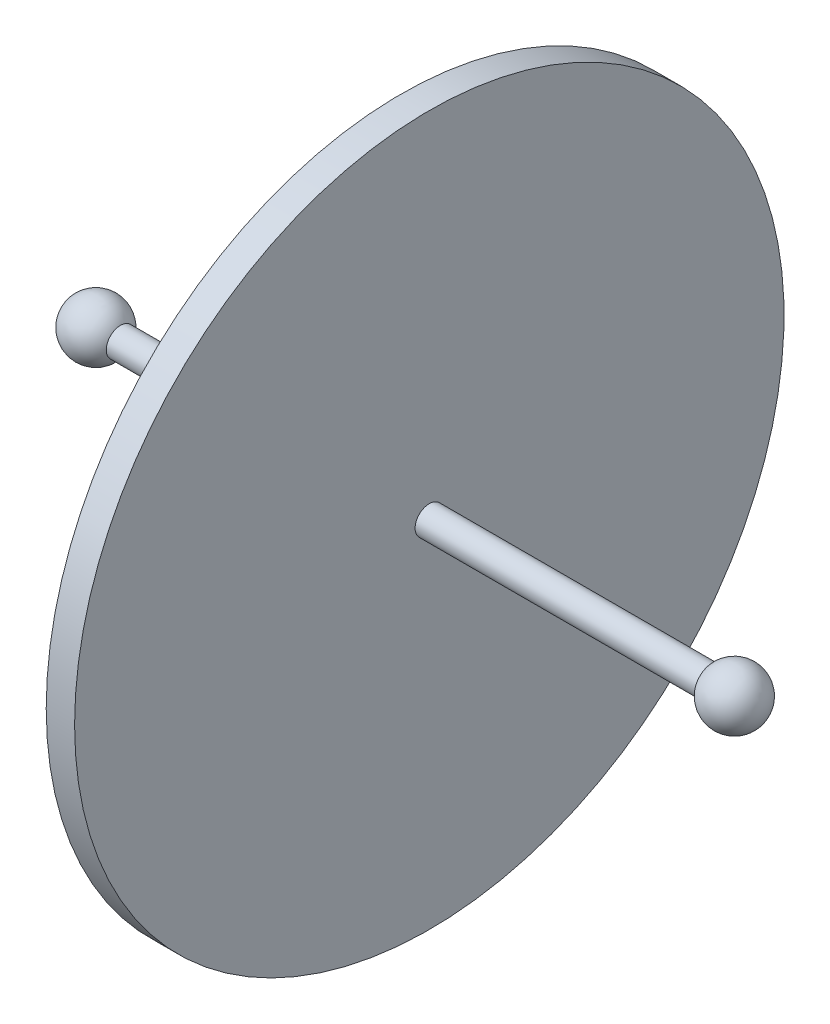
SolidWorks part; units mm, degrees
ref_plane "Plan de face" through (0, 0, 0) normal (0, 0, 1) x (1, 0, 0)
ref_plane "Plan de dessus" through (0, 0, 0) normal (0, 1, 0) x (1, 0, 0)
ref_plane "Plan de droite" through (0, 0, 0) normal (1, 0, 0) x (0, 0, -1)
sketch "Esquisse1" plane through (0, 0, 0) normal (0, 0, 1) x (1, 0, 0)
  line L0 (0, 0) -> (0, 50)
  line L1 (0, 50) -> (2, 50)
  line L2 (2, 50) -> (2, 2)
  line L3 (2, 2) -> (41.5359, 2)
  line L4 (0, 0) -> (83.6639, 0) construction
  line L5 (0, 0) -> (49, 0)
  arc A0 (41.5359, 2) -> (49, 0) centre (45, 0) cw
  point P9 (54.0899, 0)
  point P10 (40.8067, 2.1303)
  point P11 (41.5359, 2)
  point P12 (0, 0)
  dimension "D4" = 4
  dimension "D1" = 50
  dimension "D2" = 2
  dimension "D3" = 2
  dimension "D5" = 45
revolve "Révolution1" add sketch "Esquisse1" angle 360 about L4
mirror "Symétrie1" about plane through (0, 0, 0) normal (1, 0, 0) of "Révolution1"
